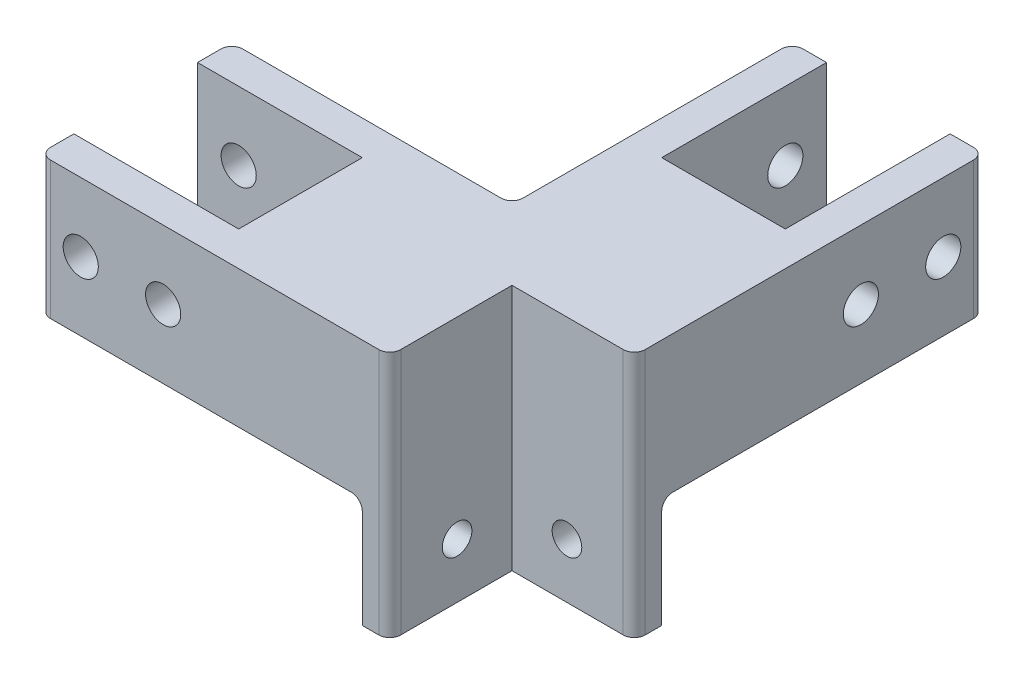
SolidWorks part; units mm, degrees
ref_plane "정면" through (0, 0, 0) normal (0, 0, 1) x (1, 0, 0)
ref_plane "윗면" through (0, 0, 0) normal (0, 1, 0) x (1, 0, 0)
ref_plane "우측면" through (0, 0, 0) normal (1, 0, 0) x (0, 0, -1)
sketch "스케치1" plane through (0, 0, 0) normal (0, 1, 0) x (1, 0, 0)
  line L0 (-17.5, 68.5) -> (-11.25, 68.5)
  line L1 (-11.25, 68.5) -> (-11.25, 38.5)
  line L2 (-11.25, 38.5) -> (11.25, 38.5)
  line L3 (11.25, 38.5) -> (11.25, 68.5)
  line L4 (11.25, 68.5) -> (17.5, 68.5)
  line L5 (17.5, 68.5) -> (17.5, -17.5)
  line L6 (17.5, -17.5) -> (-68.5, -17.5)
  line L7 (-68.5, -17.5) -> (-68.5, -11.25)
  line L8 (-68.5, -11.25) -> (-38.5, -11.25)
  line L9 (-38.5, -11.25) -> (-38.5, 11.25)
  line L10 (-38.5, 11.25) -> (-68.5, 11.25)
  line L11 (-68.5, 11.25) -> (-68.5, 17.5)
  line L12 (-68.5, 17.5) -> (-17.5, 17.5)
  line L13 (-17.5, 17.5) -> (-17.5, 68.5)
  point P14 (0, 38.5)
  point P16 (-15.41, 10.6884)
  point P17 (-21.8451, 6.5833)
  point P18 (-38.5, 0)
  point P19 (-15.5209, 16.125)
  point P20 (17.5, 54.3397)
  point P21 (-68.5, -14.375)
  point P22 (11.25, 24.8911)
  dimension "D1" = 22.5
  dimension "D2" = 22.5
  dimension "D3" = 35
  dimension "D4" = 35
  dimension "D5" = 30
  dimension "D6" = 30
  dimension "D7" = 38.5
  dimension "D8" = 38.5
extrude "보스-돌출1" add sketch "스케치1" along normal blind 25
sketch "스케치2" plane through (17.5, 0, 0) normal (1, 0, 0) x (0, 0, -1)
  line L0 (68.5, 25) -> (68.5, 0) construction
  line L1 (-17.5, 25) -> (68.5, 25) construction
  circle A0 centre (61, 12.5) radius 3.2
  circle A1 centre (46, 12.5) radius 3.2
  point P4 (0, 0)
  point P7 (0, 0)
  dimension "D3" = 6.4
  dimension "D1" = 15
  dimension "D2" = 7.5
  dimension "D4" = 12.5
extrude "컷-돌출1" cut sketch "스케치2" against normal up to surface (35 mm away) up to face at (-17.5, 12.5, -43)
sketch "스케치3" plane through (0, 0, 17.5) normal (0, 0, 1) x (1, 0, 0)
  line L0 (-68.5, 25) -> (-68.5, 0) construction
  line L1 (-68.5, 25) -> (17.5, 25) construction
  circle A0 centre (-61, 12.5) radius 3.2
  circle A1 centre (-46, 12.5) radius 3.2
  point P4 (0, 0)
  dimension "D2" = 6.4
  dimension "D1" = 15
  dimension "D3" = 7.5
  dimension "D4" = 12.5
extrude "컷-돌출2" cut sketch "스케치3" against normal up to surface (35 mm away) up to face at (-43, 12.5, -17.5)
sketch "스케치5" plane through (0, 25, 0) normal (0, 1, 0) x (1, 0, 0)
  line L1 (17.5, -17.5) -> (-4.75, -17.5)
  line L2 (17.5, -17.5) -> (17.5, 4.75)
  line L3 (17.5, 4.75) -> (-4.75, 4.75)
  line L4 (-4.75, -17.5) -> (-4.75, 4.75)
  dimension "D1" = 22.25
  dimension "D2" = 22.25
extrude "컷-돌출4" cut sketch "스케치5" against normal up to surface (25 mm away) up to face at (-25.0714, 0, -25.0714)
sketch "스케치6" plane through (0, 0, 0) normal (0, -1, 0) x (1, 0, 0)
  line L0 (-68.5, 17.5) -> (-4.75, 17.5) construction
  line L1 (-9.75, 17.5) -> (-4.75, 17.5)
  line L2 (-9.75, 17.5) -> (-9.75, -9.75)
  line L3 (-9.75, -9.75) -> (17.5, -9.75)
  line L4 (17.5, -4.75) -> (17.5, -9.75)
  line L5 (17.5, -4.75) -> (17.5, -68.5) construction
  line L6 (-4.75, 17.5) -> (-4.75, -4.75)
  line L7 (-4.75, -4.75) -> (17.5, -4.75)
  dimension "D1" = 5
  dimension "D2" = 5
extrude "보스-돌출2" add sketch "스케치6" along normal blind 20
sketch "스케치7" plane through (-4.75, 0, 0) normal (1, 0, 0) x (0, 0, -1)
  line L1 (4.75, -20) -> (4.75, 25) construction
  line L2 (4.75, -20) -> (-17.5, -20) construction
  circle A0 centre (-5.25, -10) radius 2.7
  dimension "D1" = 5.4
  dimension "D2" = 10
  dimension "D3" = 10
extrude "컷-돌출5" cut sketch "스케치7" against normal up to surface (5 mm away) up to face at (-9.75, -10, 3.875)
sketch "스케치8" plane through (0, 0, -4.75) normal (0, 0, 1) x (1, 0, 0)
  line L0 (-4.75, -20) -> (-4.75, 25) construction
  line L2 (17.5, -20) -> (-4.75, -20) construction
  circle A0 centre (5.25, -10) radius 2.7
  point P6 (7.808, -20)
  dimension "D1" = 5.4
  dimension "D2" = 10
  dimension "D3" = 10
extrude "컷-돌출6" cut sketch "스케치8" against normal up to surface (5 mm away) up to face at (3.875, -10, -9.75)
fillet "필렛1" radius 2 10 edges at (17.5, 12.5, -68.5) (-17.5, 12.5, -68.5) (17.5, 2.5, -4.75) (-4.75, 2.5, 17.5) (-68.5, 12.5, 17.5) (-68.5, 12.5, -17.5) (-17.5, 12.5, -17.5) (-9.75, -10, -9.75) (-9.75, 0, 3.875) (3.875, 0, -9.75)
